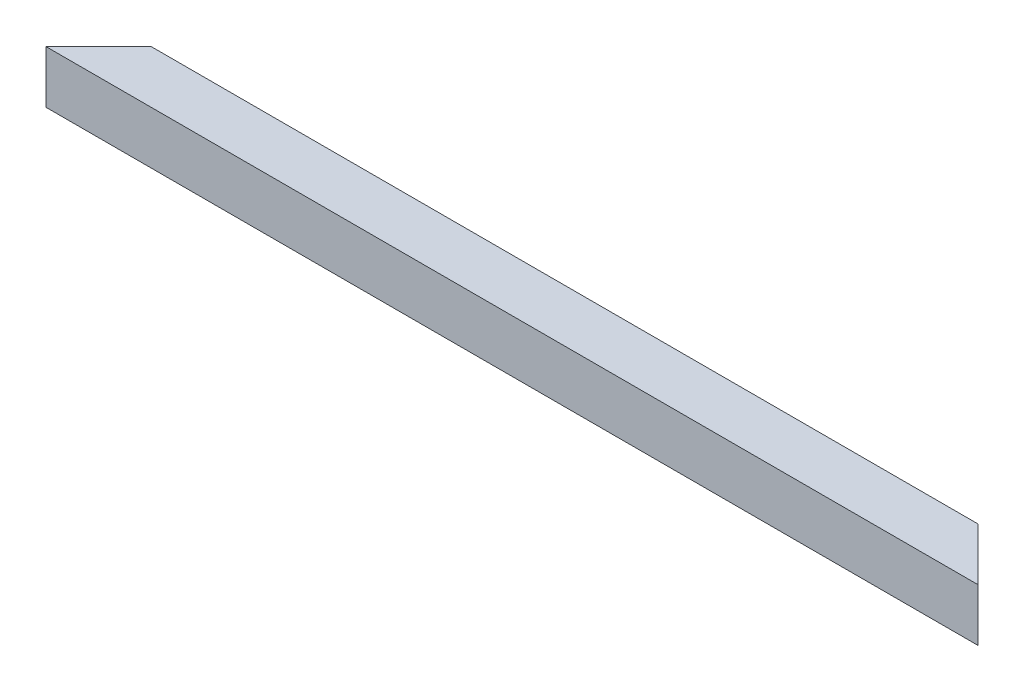
SolidWorks part; units mm, degrees
ref_plane "Alzado" through (0, 0, 0) normal (0, 0, 1) x (1, 0, 0)
ref_plane "Planta" through (0, 0, 0) normal (0, 1, 0) x (1, 0, 0)
ref_plane "Vista lateral" through (0, 0, 0) normal (1, 0, 0) x (0, 0, -1)
sketch "Sketch1" plane through (0, 0, 0) normal (0, 1, 0) x (1, 0, 0)
  line L0 (0, 0) -> (450, 0)
  line L1 (450, 0) -> (450, 25.4)
  line L2 (450, 25.4) -> (0, 25.4)
  line L3 (0, 25.4) -> (0, 0)
  dimension "D1" = 450
  dimension "D2" = 25.4
extrude "Boss-Extrude1" add sketch "Sketch1" along normal blind 25.4
sketch "Sketch2" plane through (450, 0, 0) normal (1, 0, 0) x (0, 0, -1)
  line L0 (1.2, 24.2) -> (24.2, 24.2)
  line L1 (24.2, 24.2) -> (24.2, 1.2)
  line L2 (1.2, 24.2) -> (1.2, 1.2)
  line L3 (1.2, 1.2) -> (24.2, 1.2)
  line L4 (0, 25.4) -> (0, 0) construction
  line L5 (0, 25.4) -> (25.4, 25.4) construction
  line L6 (25.4, 25.4) -> (25.4, 0) construction
  line L7 (0, 0) -> (25.4, 0) construction
  dimension "D1" = 1.2
  dimension "D2" = 1.2
  dimension "D3" = 1.2
  dimension "D4" = 1.2
extrude "Cut-Extrude1" cut sketch "Sketch2" against normal blind 450
sketch "Sketch3" plane through (0, 25.4, 0) normal (0, 1, 0) x (1, 0, 0)
  line L0 (0, 0) -> (25.4, 25.4)
  line L1 (450, 25.4) -> (0, 25.4) construction
  line L4 (0, 0) -> (0, 25.4)
  line L5 (0, 25.4) -> (25.4, 25.4)
  line L6 (450, 0) -> (424.6, 25.4)
  line L7 (424.6, 25.4) -> (450, 25.4)
  line L8 (450, 25.4) -> (450, 0)
  dimension "D1" = 25.4
  dimension "D2" = 25.4
extrude "Cut-Extrude2" cut sketch "Sketch3" against normal blind 25.4
